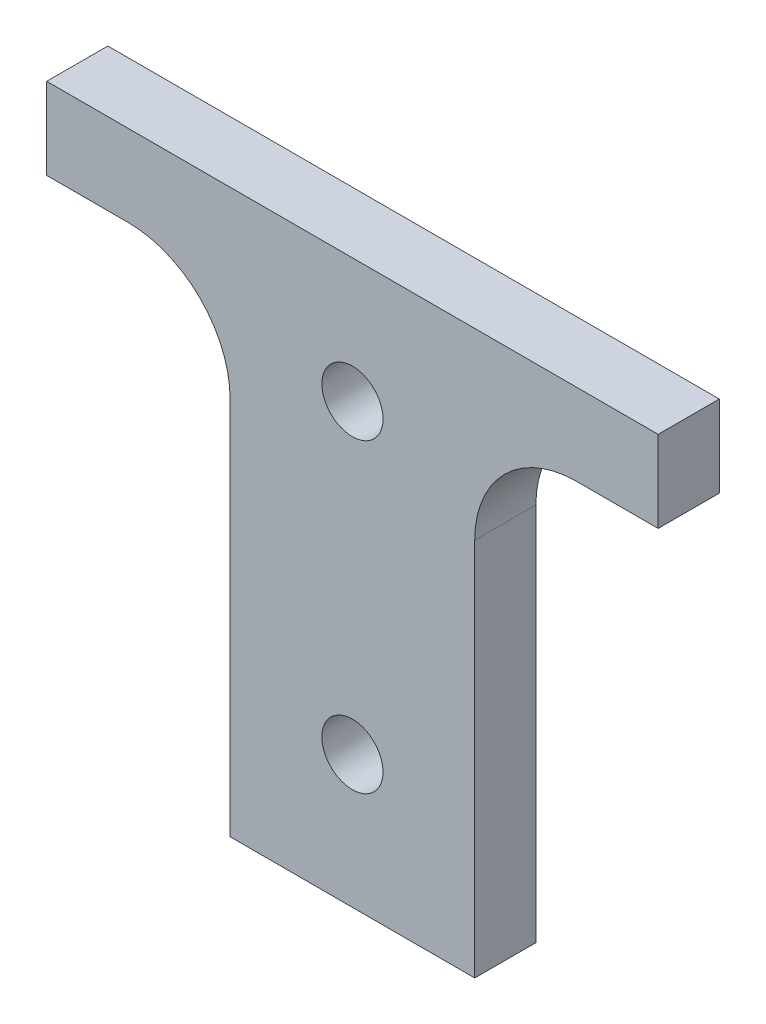
SolidWorks part; units mm, degrees
ref_plane "Front Plane" through (0, 0, 0) normal (0, 0, 1) x (1, 0, 0)
ref_plane "Top Plane" through (0, 0, 0) normal (0, 1, 0) x (1, 0, 0)
ref_plane "Right Plane" through (0, 0, 0) normal (1, 0, 0) x (0, 0, -1)
sketch "Sketch1" plane through (0, 0, 0) normal (0, 0, 1) x (1, 0, 0)
  line L0 (0, 0) -> (0, 47.9867) construction
  line L1 (6, 0) -> (-6, 0)
  line L2 (6, 0) -> (6, 23.6)
  line L4 (-6, 0) -> (-6, 23.6)
  line L5 (15, 27.6) -> (-15, 27.6)
  line L6 (-15, 27.6) -> (-15, 23.6)
  line L7 (-15, 23.6) -> (-6, 23.6)
  line L8 (15, 23.6) -> (6, 23.6)
  line L9 (15, 27.6) -> (15, 23.6)
  circle A0 centre (0, 6.5) radius 1.5
  circle A1 centre (0, 21.5) radius 1.5
  point P14 (5.4106, 27.6)
  point P17 (14.9741, 27.4084)
  dimension "D2" = 3
  dimension "D5" = 6.5
  dimension "D1" = 15
  dimension "D3" = 12
  dimension "D4" = 6.1
  dimension "D6" = 4
  dimension "D7" = 30
extrude "Boss-Extrude1" add sketch "Sketch1" along normal blind 3
fillet "Fillet1" radius 5 1 edges at (-6, 23.6, 1.5)
fillet "Fillet2" radius 5 1 edges at (6, 23.6, 1.5)
